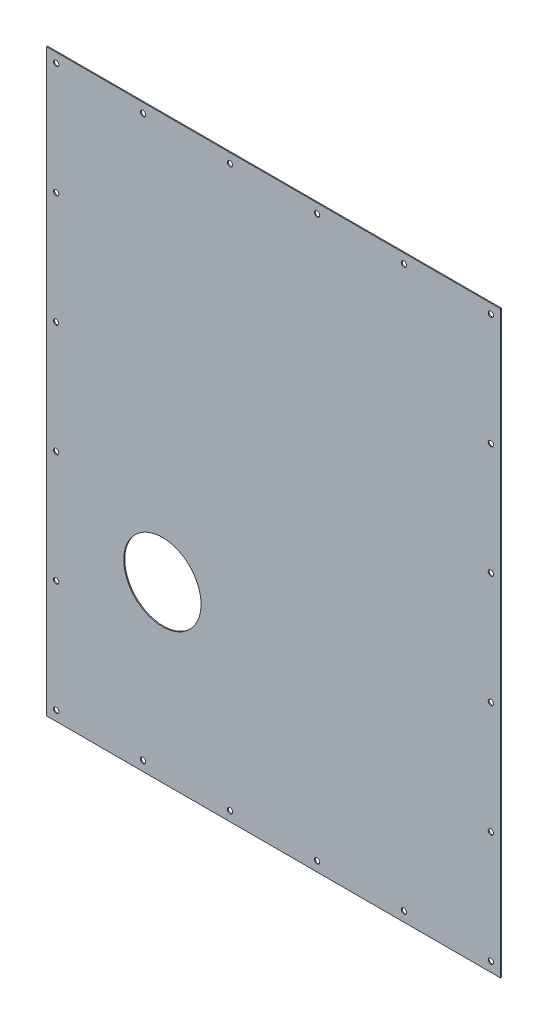
SolidWorks part; units mm, degrees
ref_plane "정면" through (0, 0, 0) normal (0, 0, 1) x (1, 0, 0)
ref_plane "윗면" through (0, 0, 0) normal (0, 1, 0) x (1, 0, 0)
ref_plane "우측면" through (0, 0, 0) normal (1, 0, 0) x (0, 0, -1)
sketch "스케치1" plane through (0, 0, 0) normal (0, 0, 1) x (1, 0, 0)
  line L1 (-235, -300) -> (235, -300)
  line L2 (-235, -300) -> (-235, 300)
  line L3 (-235, 300) -> (235, 300)
  line L4 (235, -300) -> (235, 300)
  line L5 (-235, -300) -> (235, 300) construction
  line L6 (-235, 300) -> (235, -300) construction
  line L7 (-225, -290) -> (225, -290) construction
  line L8 (-225, -290) -> (-225, 290) construction
  line L9 (-225, 290) -> (225, 290) construction
  line L10 (225, -290) -> (225, 290) construction
  line L11 (-225, -290) -> (225, 290) construction
  line L12 (-225, 290) -> (225, -290) construction
  point P0 (0, 0)
  point P6 (0, 0)
  point P11 (-45, -290)
  point P12 (-225, 290)
  point P13 (225, 290)
  point P14 (225, -290)
  point P15 (-225, -290)
  point P17 (45, -290)
  point P18 (-135, -290)
  point P19 (135, -290)
  point P20 (-225, 58)
  point P21 (-45, 290)
  point P23 (45, 290)
  point P24 (-135, 290)
  point P25 (135, 290)
  point P28 (-225, -58)
  point P29 (-225, 174)
  point P30 (-225, -174)
  point P31 (0, 0)
  point P32 (225, 58)
  point P34 (225, -58)
  point P35 (225, 174)
  point P36 (225, -174)
  point P37 (0, 0)
  point P38 (0, 0)
  point P39 (0, 0)
  point P40 (0, 0)
  point P41 (0, 0)
  point P42 (0, 0)
  point P43 (0, 0)
  point P44 (0, 0)
  point P45 (0, 0)
  dimension "D1" = 470
  dimension "D2" = 600
  dimension "D3" = 10
  dimension "D4" = 10
  dimension "D5" = 90
  dimension "D6" = 90
  dimension "D7" = 90
  dimension "D8" = 90
  dimension "D9" = 116
  dimension "a" = 116
  dimension "D10" = 116
  dimension "D11" = 116
extrude "보스-돌출1" add sketch "스케치1" along normal blind 1 contours L3 L4 L1 L2
hole_wizard "M5 여유 구멍1" positions "스케치2" profile "스케치3" hole size "M5" standard "KS" end condition through all
sketch "스케치2" plane through (0, 0, 0) normal (0, 0, -1) x (-1, 0, 0)
  point P0 (-225, 290)
  point P3 (-135, 290)
  point P6 (-45, 290)
  point P12 (45, 290)
  point P15 (135, 290)
  point P18 (225, 290)
  point P21 (225, 174)
  point P24 (225, 58)
  point P30 (225, -58)
  point P33 (225, -174)
  point P36 (225, -290)
  point P39 (-225, 174)
  point P42 (-225, 58)
  point P48 (-225, -58)
  point P51 (-225, -174)
  point P54 (-225, -290)
  point P57 (-135, -290)
  point P60 (-45, -290)
  point P66 (45, -290)
  point P69 (135, -290)
sketch "스케치3" plane through (225, 290, 0) normal (1, 0, 0) x (0, 1, 0)
  line L0 (0, 0) -> (0, 1)
  line L1 (0, 1) -> (2.75, 1)
  line L2 (2.75, 1) -> (2.75, 0)
  line L5 (2.75, 0) -> (0, 0)
  line L11 (0, -6.35) -> (0, 107.95) construction
  dimension "관통 구멍 지름" = 5.5
  dimension "관통 구멍 깊이" = 1
sketch "스케치4" plane through (0, 0, 0) normal (0, 0, -1) x (-1, 0, 0)
  line L1 (235, -300) -> (115, -300)
  line L2 (235, -300) -> (235, -120)
  line L3 (235, -120) -> (115, -120)
  line L4 (115, -300) -> (115, -120)
  line L5 (235, -300) -> (115, -120) construction
  line L6 (235, -120) -> (115, -300) construction
  circle A0 centre (115, -120) radius 40
  point P4 (175, -210)
  dimension "D1" = 80
  dimension "D2" = 180
  dimension "D3" = 120
extrude "컷-돌출1" cut sketch "스케치4" against normal blind 10 contours A0
